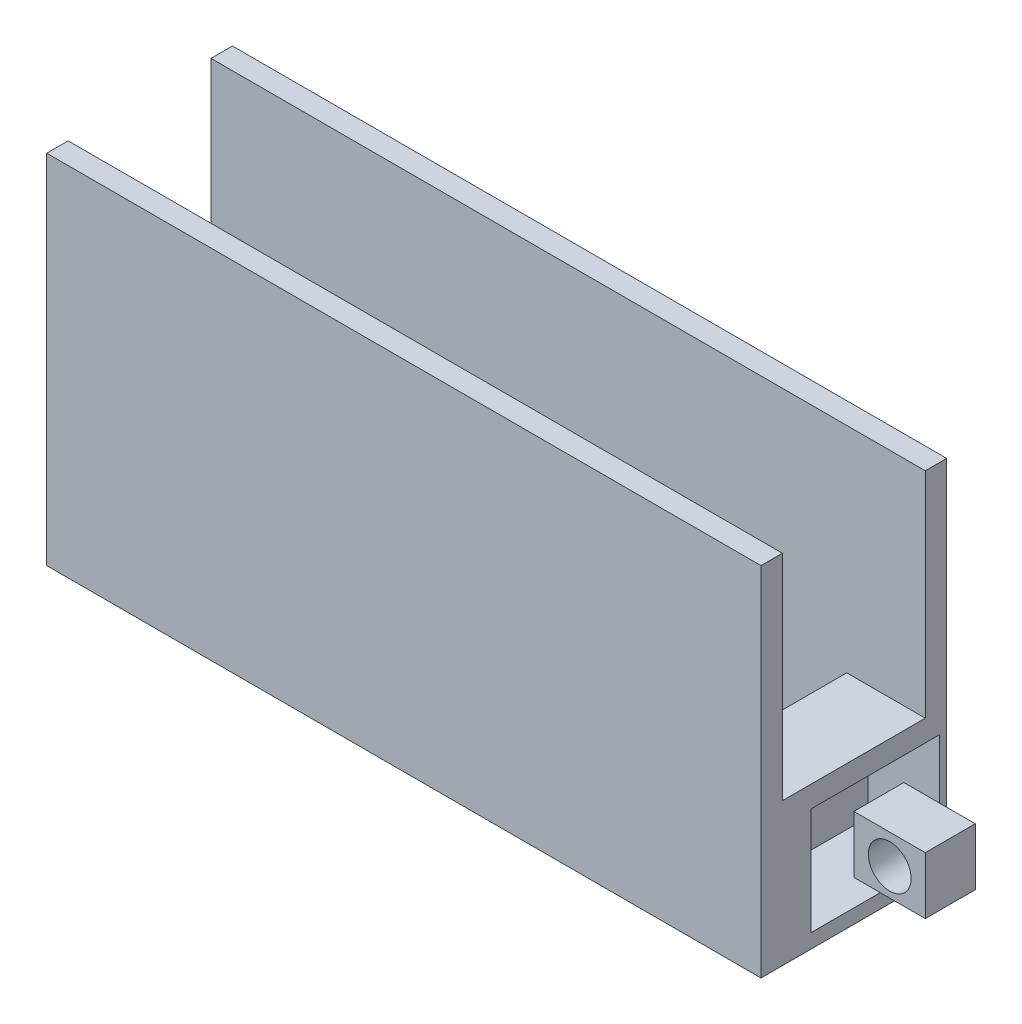
SolidWorks part; units mm, degrees
other "Markup1"
sketch "Sketch15" plane through (11, 6, 0) normal (0.9977, 0.0677, -0.0052) x (-0.0663, 0.9873, 0.1446)
ref_plane "Front Plane" through (0, 0, 0) normal (0, 0, 1) x (1, 0, 0)
ref_plane "Top Plane" through (0, 0, 0) normal (0, 1, 0) x (1, 0, 0)
ref_plane "Right Plane" through (0, 0, 0) normal (1, 0, 0) x (0, 0, -1)
sketch "Sketch19" plane through (0, 0, 0) normal (0, 1, 0) x (1, 0, 0)
  line L1 (12.528, 0) -> (22.528, 0)
  line L2 (12.528, 0) -> (12.528, -2.6)
  line L3 (12.528, -2.6) -> (22.528, -2.6)
  line L4 (22.528, 0) -> (22.528, -2.6)
  dimension "D1" = 10
  dimension "D2" = 2.6
extrude "Boss-Extrude14" add sketch "Sketch19" along normal blind 7 separate body
sketch "Sketch20" plane through (0, 7, 0) normal (0, 1, 0) x (1, 0, 0)
  line L0 (12.528, 0) -> (12.528, -2.6) construction
  line L1 (12.528, -0.3) -> (22.528, -0.3)
  line L2 (12.528, -0.3) -> (12.528, -2.3)
  line L3 (12.528, -2.3) -> (22.528, -2.3)
  line L4 (22.528, -0.3) -> (22.528, -2.3)
  line L5 (22.528, -2.6) -> (22.528, 0) construction
  line L6 (22.528, 0) -> (12.528, 0) construction
  dimension "D1" = 0.3
  dimension "D2" = 2
extrude "Cut-Extrude8" cut sketch "Sketch20" against normal blind 5
sketch "Sketch21" plane through (22.528, 0, 0) normal (1, 0, 0) x (0, 0, -1)
  line L0 (-2.6, 0) -> (0, 0) construction
  line L1 (-1.3, 0.57) -> (-0.6, 0.57)
  line L2 (-1.3, 0.57) -> (-1.3, 1.37)
  line L3 (-1.3, 1.37) -> (-0.6, 1.37)
  line L4 (-0.6, 0.57) -> (-0.6, 1.37)
  line L5 (0, 7) -> (0, 0) construction
  dimension "D1" = 0.8
  dimension "D2" = 0.7
  dimension "D3" = 0.57
  dimension "D4" = 0.6
extrude "Boss-Extrude15" add sketch "Sketch21" along normal blind 1
sketch "Sketch22" plane through (0, 0, 1.3) normal (0, 0, 1) x (1, 0, 0)
  line L0 (23.0327, 1.3589) -> (23.028, 0.57) construction
  line L1 (23.528, 0.57) -> (22.528, 0.57) construction
  circle A0 centre (23.0303, 0.9551) radius 0.3
extrude "Cut-Extrude9" cut sketch "Sketch22" against normal blind 1
sketch "Sketch23" plane through (22.528, 0, 0) normal (1, 0, 0) x (0, 0, -1)
  line L0 (0, 7) -> (0, 0) construction
  line L1 (-1.9, 1.7) -> (-0.1, 1.7)
  line L2 (-1.9, 1.7) -> (-1.9, 0.2)
  line L3 (-1.9, 0.2) -> (-0.1, 0.2)
  line L4 (-0.1, 1.7) -> (-0.1, 0.2)
  line L5 (-2.6, 0) -> (0, 0) construction
  dimension "D1" = 1.8
  dimension "D2" = 0.1
  dimension "D3" = 0.2
extrude "Cut-Extrude10" cut sketch "Sketch23" against normal blind 1
sketch "Sketch24" plane through (0, 2, 0) normal (0, 1, 0) x (1, 0, 0)
  line L0 (12.528, -0.3) -> (12.528, -2.3) construction
  line L1 (12.628, -0.4) -> (21.428, -0.4)
  line L2 (12.628, -0.4) -> (12.628, -2.2)
  line L3 (12.628, -2.2) -> (21.428, -2.2)
  line L4 (21.428, -0.4) -> (21.428, -2.2)
  line L5 (22.528, -0.3) -> (12.528, -0.3) construction
  line L6 (12.528, -2.3) -> (22.528, -2.3) construction
  dimension "D1" = 8.8
  dimension "D2" = 0.1
  dimension "D3" = 0.1
  dimension "D4" = 0.1
extrude "Cut-Extrude11" cut sketch "Sketch24" against normal blind 10
sketch "Sketch25" plane through (12.528, 0, 0) normal (-1, 0, 0) x (0, 0, 1)
  line L0 (0, 0) -> (2.6, 0) construction
  line L1 (0.3, 2) -> (2.3, 2)
  line L2 (0.3, 2) -> (0.3, 0.2)
  line L3 (0.3, 0.2) -> (2.3, 0.2)
  line L4 (2.3, 2) -> (2.3, 0.2)
  dimension "D1" = 2
  dimension "D2" = 0.2
extrude "Cut-Extrude13" cut sketch "Sketch25" against normal blind 8.9
sketch "Sketch26" plane through (0, 0, 0) normal (0, 0, -1) x (-1, 0, 0)
  line L0 (-12.528, 7) -> (-12.528, 0) construction
  line L1 (-22.528, 7) -> (-12.528, 7)
  line L2 (-22.528, 7) -> (-22.528, 5)
  line L3 (-22.528, 5) -> (-12.528, 5)
  line L4 (-12.528, 7) -> (-12.528, 5)
  dimension "D1" = 2
extrude "Cut-Extrude14" cut sketch "Sketch26" against normal blind 10
